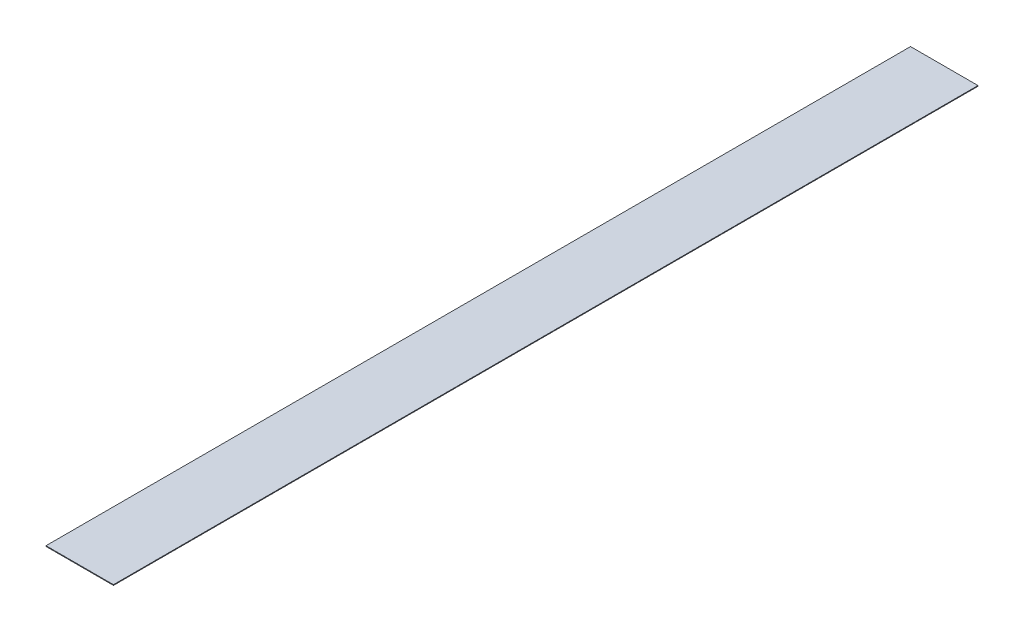
SolidWorks part; units mm, degrees
ref_plane "Front Plane" through (0, 0, 0) normal (0, 0, 1) x (1, 0, 0)
ref_plane "Top Plane" through (0, 0, 0) normal (0, 1, 0) x (1, 0, 0)
ref_plane "Right Plane" through (0, 0, 0) normal (1, 0, 0) x (0, 0, -1)
sketch "Sketch1" plane through (0, 0, 0) normal (0, 1, 0) x (1, 0, 0)
  line L1 (-25.4, 0) -> (25.4, 0)
  line L2 (-25.4, 0) -> (-25.4, 650.875)
  line L3 (-25.4, 650.875) -> (25.4, 650.875)
  line L4 (25.4, 0) -> (25.4, 650.875)
  dimension "D1" = 50.8
  dimension "D2" = 650.875
extrude "Boss-Extrude1" add sketch "Sketch1" along normal blind 0.508
